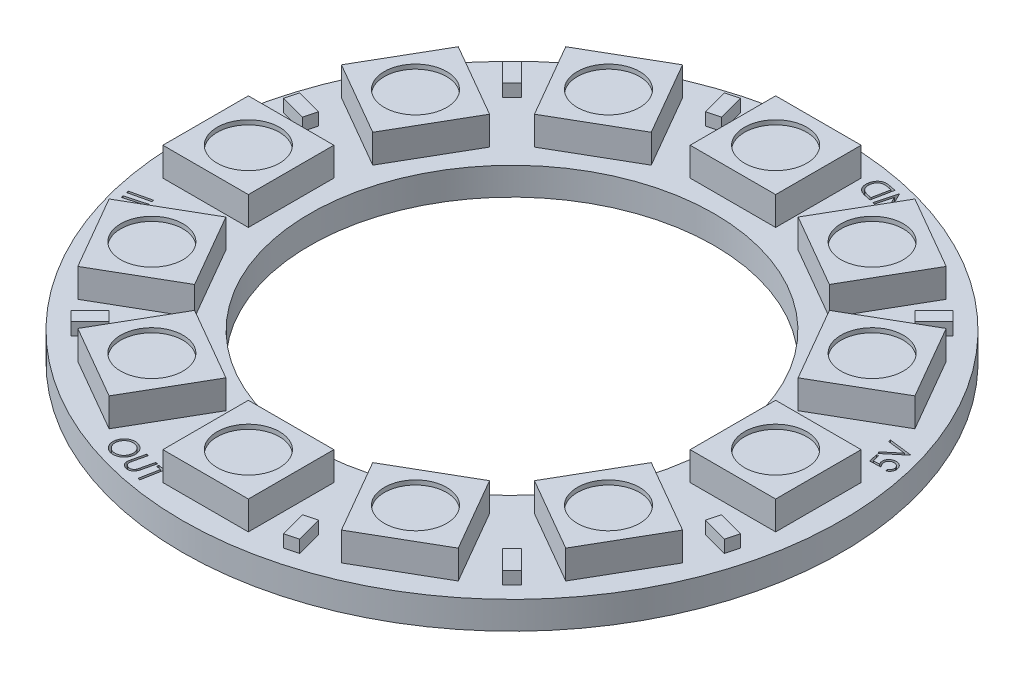
SolidWorks part; units mm, degrees
ref_plane "Front Plane" through (0, 0, 0) normal (0, 0, 1) x (1, 0, 0)
ref_plane "Top Plane" through (0, 0, 0) normal (0, 1, 0) x (1, 0, 0)
ref_plane "Right Plane" through (0, 0, 0) normal (1, 0, 0) x (0, 0, -1)
sketch "Sketch1" plane through (0, 0, 0) normal (0, 1, 0) x (1, 0, 0)
  circle A0 centre (0, 0) radius 11.35
  circle A1 centre (0, 0) radius 18.5
  dimension "D1" = 22.7
  dimension "D2" = 37
  dimension "D3" = 7.15
extrude "Boss-Extrude1" add sketch "Sketch1" along normal blind 1.55
sketch "Sketch2" plane through (0, 1.55, 0) normal (0, 1, 0) x (1, 0, 0)
  line L1 (-2.4, 12.4) -> (2.4, 12.4)
  line L2 (-2.4, 12.4) -> (-2.4, 17.2)
  line L3 (-2.4, 17.2) -> (2.4, 17.2)
  line L4 (2.4, 12.4) -> (2.4, 17.2)
  line L5 (-2.4, 12.4) -> (2.4, 17.2) construction
  line L6 (-2.4, 17.2) -> (2.4, 12.4) construction
  circle A1 centre (0, 0) radius 18.5 construction
  circle A4 centre (0, 0) radius 18.5 construction
  point P0 (0, 14.8)
  dimension "D1" = 4.8
  dimension "D2" = 4.8
  dimension "D3" = 1.3
extrude "Boss-Extrude2" add sketch "Sketch2" along normal blind 1.6
sketch "Sketch5" plane through (0, 3.15, 0) normal (0, 1, 0) x (1, 0, 0)
  line L0 (2.4, 17.2) -> (-2.4, 17.2) construction
  line L1 (2.4, 12.4) -> (2.4, 17.2) construction
  circle A0 centre (0, 14.8) radius 1.75
  point P5 (0, 17.2)
  point P8 (2.4, 14.8)
  dimension "D1" = 3.5
extrude "Cut-Extrude2" cut sketch "Sketch5" against normal blind 0.25
pattern_circular "CirPattern1" count 12 over 360 about axis through (0, 0, 0) along (0, 1, 0) of "Boss-Extrude2", "Cut-Extrude2"
sketch "Sketch3" plane through (0, 1.55, 0) normal (0, 1, 0) x (1, 0, 0)
  line L0 (-4.5033, 15.3578) -> (-4.8916, 16.8066)
  line L1 (-4.5033, 15.3578) -> (-3.7789, 15.5519)
  line L2 (-4.8916, 16.8066) -> (-4.1671, 17.0008)
  line L3 (-3.7789, 15.5519) -> (-4.1671, 17.0008)
  line L4 (-2.9376, 10.9633) -> (-4.7882, 17.8696) construction
  line L5 (-5.7541, 17.6108) -> (-3.8222, 18.1284) construction
  line L6 (-4.1215, 11.9387) -> (-2.4, 12.4) construction
  line L7 (-3.9035, 10.7044) -> (-1.9717, 11.2221) construction
  circle A2 centre (0, 0) radius 18.5 construction
  circle A3 centre (0, 0) radius 11.35 construction
  point P10 (-4.5293, 16.9037)
  point P11 (-3.2608, 12.1694)
  point P14 (-4.7882, 17.8696)
  point P17 (-2.9376, 10.9633)
  dimension "D1" = 0.75
  dimension "D2" = 1.5
  dimension "D3" = 1
  dimension "D4" = 2
extrude "Boss-Extrude3" add sketch "Sketch3" along normal offset from surface (0.7 mm away) 2.25 up to face at (0, 0, 18.5)
pattern_circular "CirPattern2" count 12 over 360 about axis through (0, 1.55, 0) along (0, -1, 0) skipping 1, 3, 7, 9 of "Boss-Extrude3"
sketch "Sketch4" plane through (0, 1.55, 0) normal (0, 1, 0) x (1, 0, 0)
  circle A2 centre (0, 0) radius 18
  circle A3 centre (0, 0) radius 18 construction
  text T0 "        5V                                  GND                                                                            IN                                    OUT" font "Century Gothic" height 1.2
  dimension "D1" = 0.5
extrude "Cut-Extrude1" cut sketch "Sketch4" against normal blind 0.5
